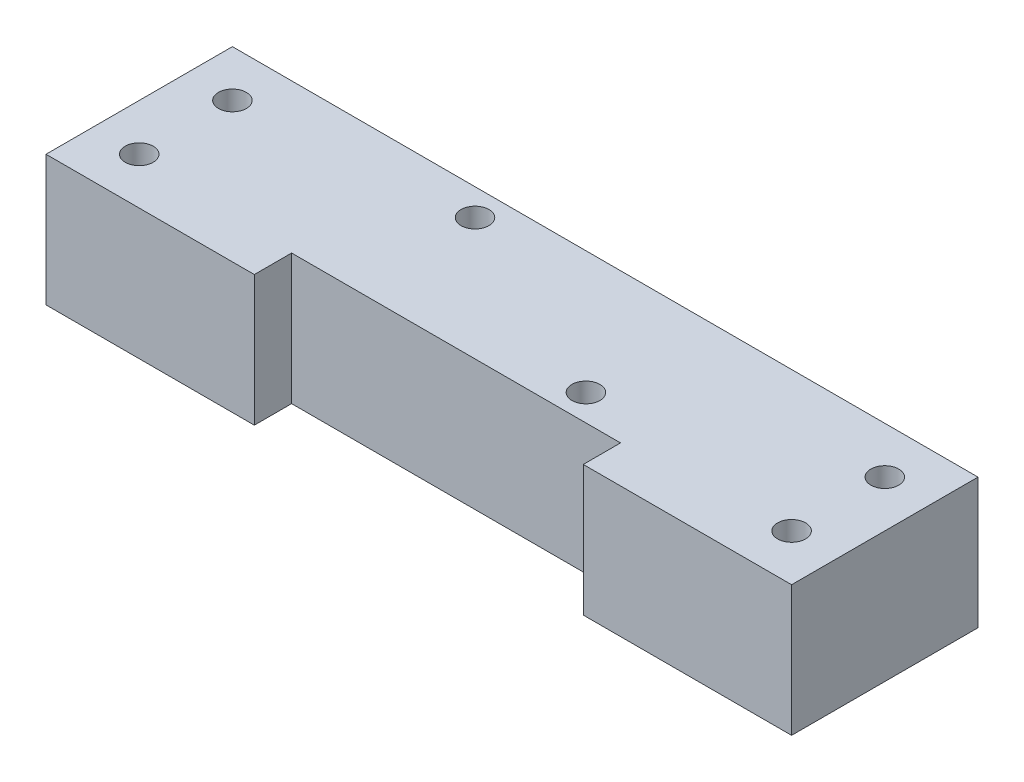
SolidWorks part; units mm, degrees
ref_plane "Front Plane" through (0, 0, 0) normal (0, 0, 1) x (1, 0, 0)
ref_plane "Top Plane" through (0, 0, 0) normal (0, 1, 0) x (1, 0, 0)
ref_plane "Right Plane" through (0, 0, 0) normal (1, 0, 0) x (0, 0, -1)
sketch "Sketch1" plane through (0, 0, 0) normal (0, 0, 1) x (1, 0, 0)
  line L1 (0, 0) -> (80, 0)
  line L2 (0, 0) -> (0, 14)
  line L3 (0, 14) -> (80, 14)
  line L4 (80, 0) -> (80, 14)
  dimension "D1" = 80
  dimension "D2" = 14
extrude "Boss-Extrude1" add sketch "Sketch1" along normal blind 20
sketch "Sketch2" plane through (0, 0, 20) normal (0, 0, 1) x (1, 0, 0)
  line L0 (40, 14) -> (40, -10.2697) construction
  line L1 (80, 14) -> (0, 14) construction
  line L2 (0, 0) -> (80, 0) construction
  line L3 (22.354, 14) -> (57.646, 14)
  line L4 (22.354, 14) -> (22.354, 0)
  line L5 (22.354, 0) -> (57.646, 0)
  line L6 (57.646, 14) -> (57.646, 0)
  dimension "D1" = 22.354
  dimension "D2" = 22.354
extrude "Cut-Extrude1" cut sketch "Sketch2" against normal blind 4
sketch "Sketch3" plane through (0, 14, 0) normal (0, 1, 0) x (1, 0, 0)
  line L0 (0, -10) -> (30.0453, -10) construction
  line L1 (0, -20) -> (0, 0) construction
  line L2 (80, 0) -> (0, 0) construction
  line L3 (40, 0) -> (40, -27.263) construction
  circle A0 centre (5, -5) radius 1.5
  circle A1 centre (5, -15) radius 1.5
  circle A2 centre (75, -15) radius 1.5
  circle A3 centre (75, -5) radius 1.5
  dimension "D2" = 3
  dimension "D1" = 5
  dimension "D3" = 5
extrude "Cut-Extrude2" cut sketch "Sketch3" against normal blind 14
sketch "Sketch4" plane through (0, 14, 0) normal (0, 1, 0) x (1, 0, 0)
  line L0 (80, 0) -> (0, 0) construction
  line L1 (0, -20) -> (0, 0) construction
  circle A0 centre (28.9, -2.87) radius 1.5
  circle A1 centre (51.1, -13.17) radius 1.5
  dimension "D1" = 3
  dimension "D2" = 3
  dimension "D3" = 2.87
  dimension "D4" = 28.9
  dimension "D5" = 13.17
  dimension "D6" = 51.1
extrude "Cut-Extrude3" cut sketch "Sketch4" against normal blind 8
